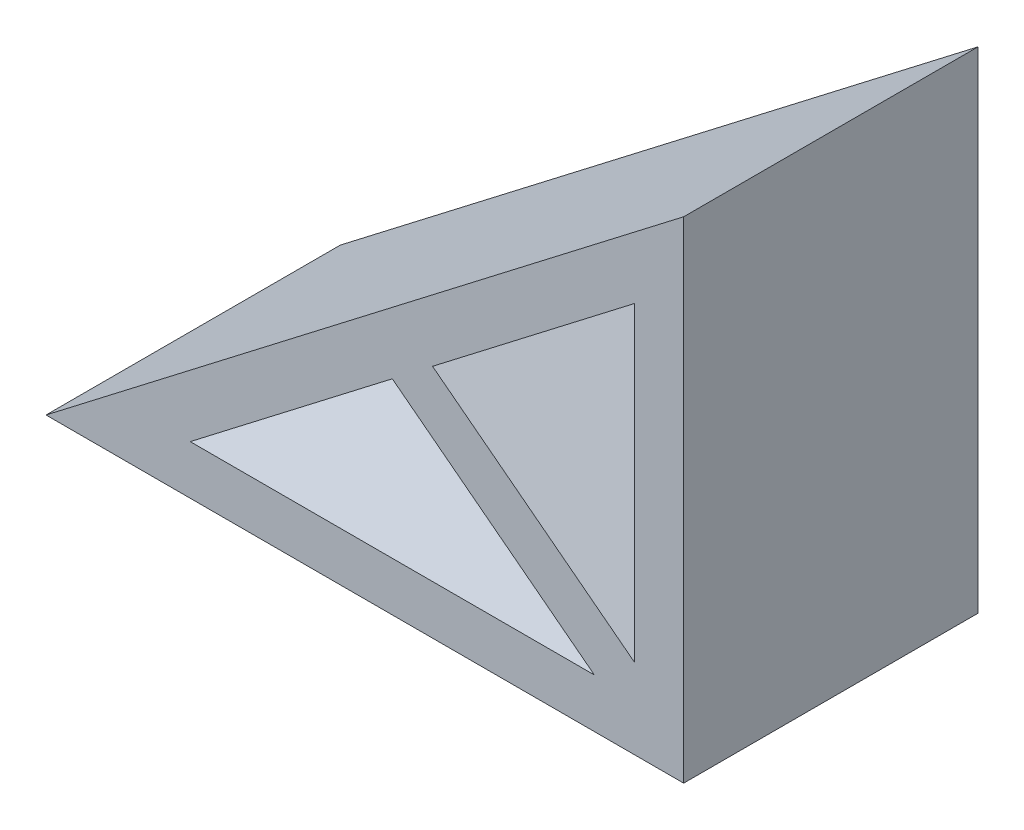
SolidWorks part; units mm, degrees
ref_plane "Front" through (0, 0, 0) normal (0, 0, 1) x (1, 0, 0)
ref_plane "Top" through (0, 0, 0) normal (0, 1, 0) x (1, 0, 0)
ref_plane "Right" through (0, 0, 0) normal (1, 0, 0) x (0, 0, -1)
sketch "Sketch1" plane through (0, 0, 0) normal (0, 0, 1) x (1, 0, 0)
  line L0 (0, 0) -> (-41.275, 0)
  line L1 (-41.275, 0) -> (0, 31.75)
  line L2 (0, 31.75) -> (0, 0)
  dimension "D1" = 31.75
  dimension "D2" = 41.275
extrude "Boss-Extrude1" add sketch "Sketch1" along normal mid plane 19.05
sketch "Sketch2" plane through (0, 0, 0) normal (0, 0, 1) x (1, 0, 0)
  line L3 (-3.175, 3.175) -> (-17.5576, 14.2385) construction
  line L4 (-3.175, 5.1778) -> (-16.2557, 15.2399)
  line L5 (-5.7787, 3.175) -> (-18.8594, 13.2371)
  line L6 (-3.175, 3.175) -> (-3.175, 25.302)
  line L7 (-3.175, 25.302) -> (-31.9401, 3.175)
  line L8 (-31.9401, 3.175) -> (-3.175, 3.175)
  line L9 (-3.175, 5.1778) -> (-3.175, 25.302)
  line L10 (-3.175, 25.302) -> (-16.2557, 15.2399)
  line L11 (-31.9401, 3.175) -> (-5.7787, 3.175)
  line L12 (-5.7787, 3.175) -> (-3.8429, 5.6916) construction
  line L13 (-3.175, 3.175) -> (0, 3.175) construction
  line L14 (0, 0) -> (0, 31.75) construction
  line L15 (-16.2557, 15.2399) -> (-17.5576, 14.2385) construction
  line L16 (-18.8594, 13.2371) -> (-31.9401, 3.175)
  line L17 (-17.5576, 14.2385) -> (-18.8594, 13.2371) construction
  line L18 (-3.175, 3.175) -> (-3.175, 5.1778) construction
  line L19 (-5.7787, 3.175) -> (-3.175, 3.175) construction
  point P9 (-4.8108, 4.4333)
  dimension "D1" = 3.175
extrude "Cut-Extrude1" cut sketch "Sketch2" against normal through all both and the other way through all
sketch "Sketch3" plane through (0, 0, 0) normal (0, 1, 0) x (1, 0, 0)
  line L0 (0, -9.525) -> (-41.275, -9.525) construction
  line L1 (-41.275, -9.525) -> (-41.275, 9.525) construction
  circle A0 centre (17.0656, -26.9875) radius 6.35
  dimension "D1" = 12.7
  dimension "D2" = 17.4625
  dimension "D3" = 58.3406
